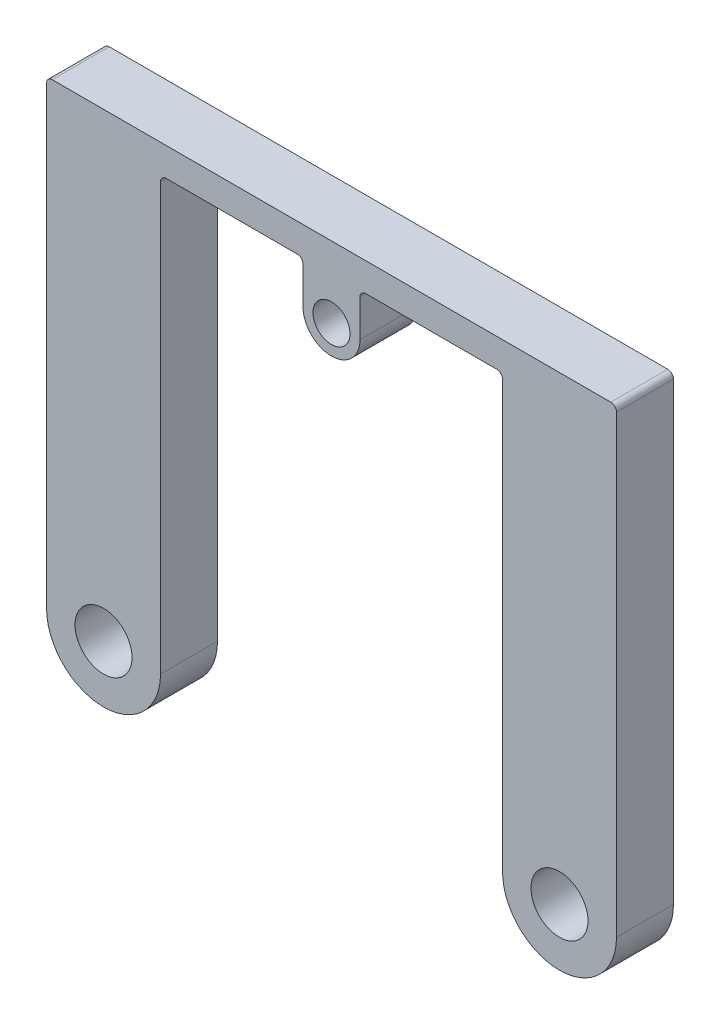
SolidWorks part; units mm, degrees
ref_plane "Front Plane" through (0, 0, 0) normal (0, 0, 1) x (1, 0, 0)
ref_plane "Top Plane" through (0, 0, 0) normal (0, 1, 0) x (1, 0, 0)
ref_plane "Right Plane" through (0, 0, 0) normal (1, 0, 0) x (0, 0, -1)
sketch "Sketch1" plane through (0, 0, 0) normal (0, 0, 1) x (1, 0, 0)
  line L0 (0, -49.9495) -> (0, 49.9495) construction
  line L1 (-50, 0) -> (-50, 80.8172)
  line L2 (-50, 80.8172) -> (-30, 80.8172)
  line L3 (-30, 80.8172) -> (-30, 0)
  line L4 (30, 0) -> (30, 80.8172)
  line L5 (30, 80.8172) -> (50, 80.8172)
  line L6 (50, 80.8172) -> (50, 0)
  line L7 (-30, 75.8172) -> (30, 75.8172)
  line L8 (-30, 80.8172) -> (30, 80.8172)
  circle A0 centre (-40, 0) radius 10
  circle A1 centre (40, 0) radius 10
  circle A2 centre (-40, 0) radius 5
  circle A3 centre (40, 0) radius 5
  dimension "D2" = 20
  dimension "D3" = 10
  dimension "D1" = 80
  dimension "D4" = 5
extrude "Boss-Extrude1" add sketch "Sketch1" along normal mid plane 10 contours A0 L3 L2 L1 | L8 L3 L7 L4 | L4 A1 L6 L5 | A0 A2 | A1 A3
sketch "Sketch2" plane through (0, 0, 5) normal (0, 0, 1) x (1, 0, 0)
  line L0 (-5, 68.3172) -> (-5, 75.8172)
  line L1 (-30, 75.8172) -> (30, 75.8172) construction
  line L2 (5, 68.3172) -> (5, 75.8172)
  line L3 (0, 0) -> (0, 68.3172) construction
  circle A0 centre (0, 68.3172) radius 3.25
  circle A1 centre (0, 68.3172) radius 5
  dimension "D1" = 10
  dimension "D2" = 6.5
  dimension "D3" = 7.5
extrude "Boss-Extrude2" add sketch "Sketch2" against normal up to surface (10 mm away)
fillet "Fillet1" radius 1 6 edges at (-50, 80.8172, 0) (50, 80.8172, 0) (-30, 75.8172, 0) (-5, 75.8172, 0) (5, 75.8172, 0) (30, 75.8172, 0)
